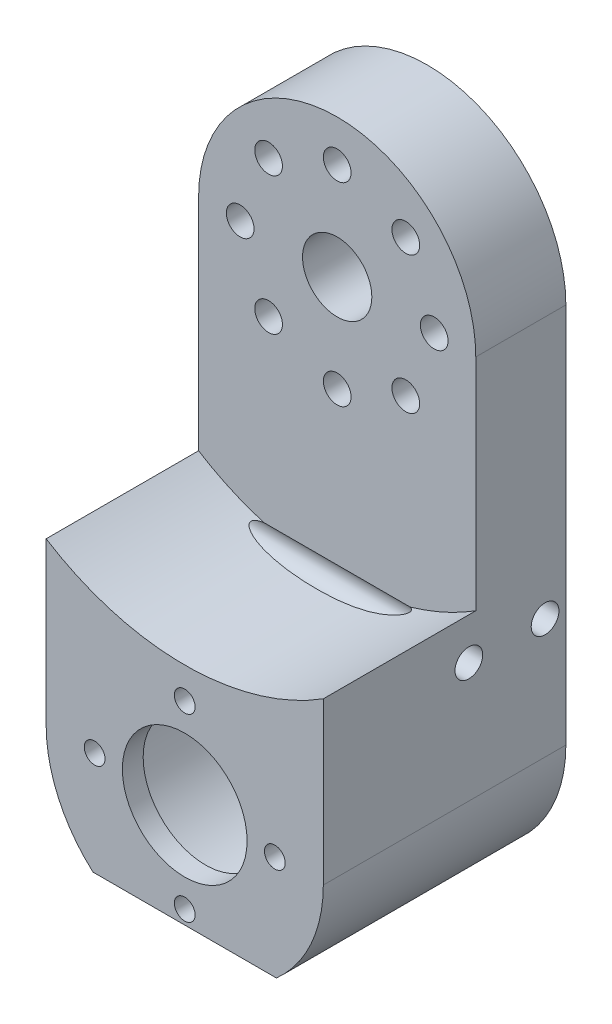
SolidWorks part; units mm, degrees
ref_plane "Plan de face" through (0, 0, 0) normal (0, 0, 1) x (1, 0, 0)
ref_plane "Plan de dessus" through (0, 0, 0) normal (0, 1, 0) x (1, 0, 0)
ref_plane "Plan de droite" through (0, 0, 0) normal (1, 0, 0) x (0, 0, -1)
sketch "Esquisse1" plane through (0, 0, 0) normal (0, 0, 1) x (1, 0, 0)
  line L1 (20, -20) -> (20, -75)
  line L3 (0, 0) -> (0, 23.2042) construction
  line L4 (-20, -20) -> (-20, -75)
  arc A0 (-20, -75) -> (20, -75) centre (0, -75) ccw
  arc A1 (20, -20) -> (-20, -20) centre (0, -20) ccw
  circle A2 centre (0, -75) radius 15
  circle A3 centre (0, -20) radius 5
  circle A4 centre (-14, -20) radius 2
  circle A5 centre (-9.8995, -10.1005) radius 2
  circle A6 centre (0, -6) radius 2
  circle A7 centre (9.8995, -10.1005) radius 2
  circle A8 centre (14, -20) radius 2
  circle A9 centre (9.8995, -29.8995) radius 2
  circle A10 centre (0, -34) radius 2
  circle A11 centre (-9.8995, -29.8995) radius 2
  dimension "D1" = 30
extrude "Extrusion1" add sketch "Esquisse1" along normal blind 13
sketch "Esquisse2" plane through (0, 0, 13) normal (0, 0, 1) x (1, 0, 0)
  line L0 (-20, -75) -> (-20, -51.7214)
  line L3 (20, -75) -> (20, -51.7214)
  arc A0 (-20, -75) -> (20, -75) centre (0, -75) ccw
  circle A1 centre (0, -75) radius 9
  arc A2 (-20, -51.7214) -> (20, -51.7214) centre (0, -20) ccw
  circle A3 centre (0, -62) radius 1.5
  circle A4 centre (0, -88) radius 1.5
  circle A5 centre (-13, -75) radius 1.5
  circle A6 centre (13, -75) radius 1.5
extrude "Extrusion2" add sketch "Esquisse2" along normal blind 22
sketch "Esquisse3" plane through (0, 0, 13) normal (0, 0, -1) x (-1, 0, 0)
  circle A0 centre (0, -75) radius 15
extrude "Extrusion3" cut sketch "Esquisse3" against normal blind 19
sketch "Esquisse4" plane through (0, 0, 0) normal (1, 0, 0) x (0, 0, -1)
  line L0 (-35, -95) -> (-30, -95)
  line L1 (-35, -95) -> (0, -95) construction
  line L2 (-35, -95) -> (-35, -90)
  line L3 (-35, -75) -> (-35, -95) construction
  line L4 (-35, -90) -> (-30, -95)
extrude "Extrusion4" cut sketch "Esquisse4" against normal through all and the other way through all
sketch "Esquisse5" plane through (-20, 0, 0) normal (-1, 0, 0) x (0, 0, 1)
  circle A0 centre (14, -57.7214) radius 2
  circle A2 centre (3, -57.7214) radius 2
extrude "Extrusion5" cut sketch "Esquisse5" against normal up to next
